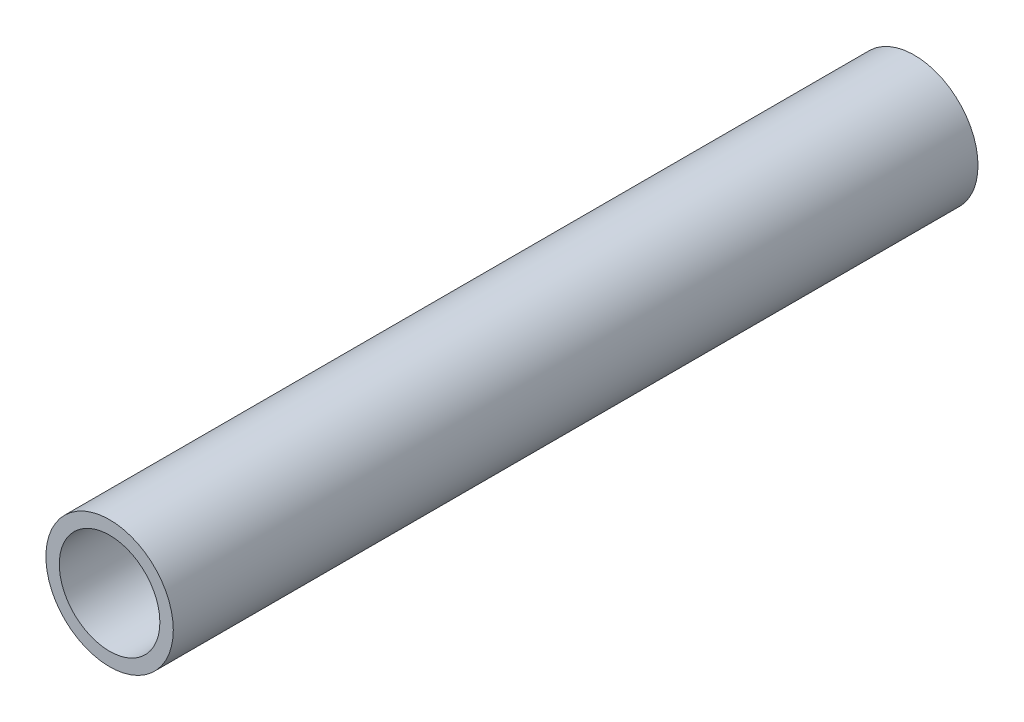
SolidWorks part; units mm, degrees
ref_plane "Front Plane" through (0, 0, 0) normal (0, 0, 1) x (1, 0, 0)
ref_plane "Top Plane" through (0, 0, 0) normal (0, 1, 0) x (1, 0, 0)
ref_plane "Right Plane" through (0, 0, 0) normal (1, 0, 0) x (0, 0, -1)
sketch "PipeSketch" plane through (0, 0, 0) normal (0, 0, 1) x (1, 0, 0)
  circle A0 centre (0, 0) radius 24.13
  circle A1 centre (0, 0) radius 19.05
  dimension "InnerDiameter" = 38.1
  dimension "OuterDiameter" = 48.26
extrude "Extrusion" add sketch "PipeSketch" along normal blind 304.8 contours A0 A1
sketch "FilterSketch" plane through (0, 0, 0) normal (0, 0, 1) x (1, 0, 0)
  circle A0 centre (0, 0) radius 19.05
  dimension "NominalDiameter" = 38.1
